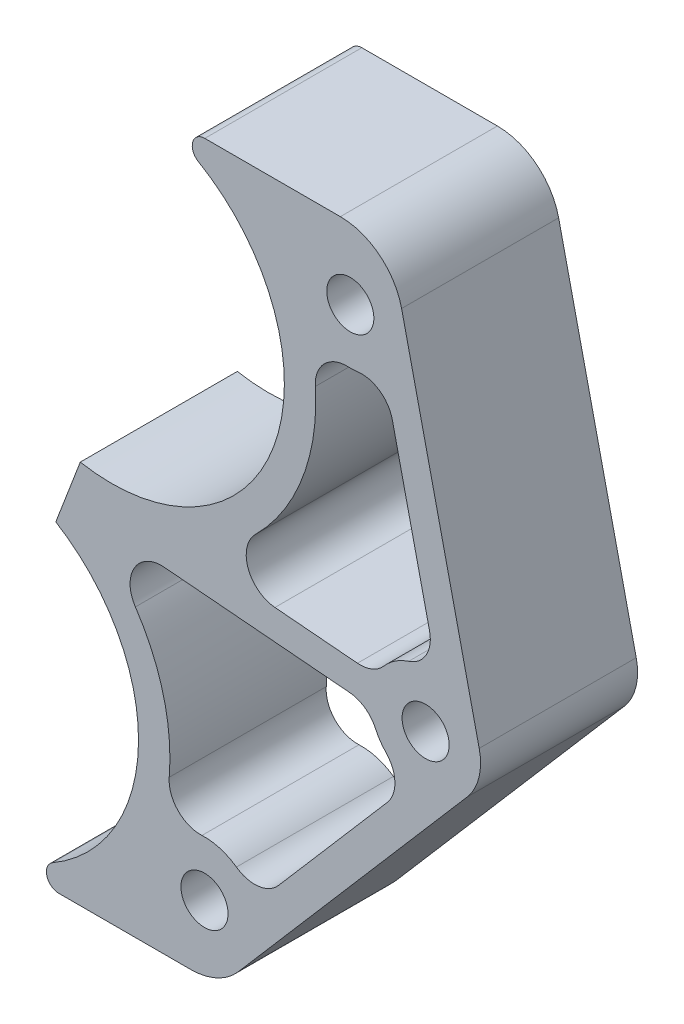
SolidWorks part; units mm, degrees
material "6061-T6 (SS)"
ref_plane "Front Plane" through (0, 0, 0) normal (0, 0, 1) x (1, 0, 0)
ref_plane "Top Plane" through (0, 0, 0) normal (0, 1, 0) x (1, 0, 0)
ref_plane "Right Plane" through (0, 0, 0) normal (1, 0, 0) x (0, 0, -1)
sketch "Sketch1" plane through (0, 0, 0) normal (0, 0, 1) x (1, 0, 0)
  line L0 (-29.4864, -77.1042) -> (0, 0) construction
  line L1 (-17.0114, -44.4832) -> (-12.475, -32.621)
  line L2 (-29.4864, -112.0292) -> (-29.4864, -117.5664)
  line L3 (-29.4864, -117.5664) -> (41.2306, -117.5664)
  line L4 (73.869, -111.2164) -> (73.869, -30.1792) construction
  line L5 (17.0334, -117.5664) -> (71.9024, -53.8526)
  line L6 (55.3346, 39.5732) -> (0, 39.5732)
  line L7 (0, 39.5732) -> (0, 34.925)
  line L8 (74.3193, -44.1435) -> (55.3346, 39.5732)
  line L9 (74.3193, -44.1435) -> (58.9814, 23.4919) construction
  line L10 (-6.2488, -111.2164) -> (41.2306, -111.2164) construction
  line L11 (10.6196, -44.2711) -> (48.1064, -47.4625)
  line L12 (33.0193, -40.1207) -> (49.7043, -41.5411)
  line L13 (27.1941, -105.7679) -> (71.9024, -53.8526) construction
  line L14 (33.7304, -88.4469) -> (55.7427, -62.8862)
  line L16 (64.2806, -28.5883) -> (56.7506, 4.6169)
  line L17 (-8.9876, -41.2793) -> (-8.6366, -40.3613) construction
  line L18 (41.2306, -111.2164) -> (73.869, -111.2164) construction
  line L19 (73.869, -30.1792) -> (73.869, 33.2232) construction
  line L20 (73.869, 33.2232) -> (24.4917, 33.2232) construction
  line L21 (24.4917, 33.2232) -> (24.4917, 33.2232) construction
  line L22 (-6.2488, -111.2164) -> (-6.2488, -111.2164) construction
  line L23 (80.219, 39.5732) -> (0, 39.5732) construction
  line L24 (68.1266, -45.5478) -> (52.7887, 22.0876) construction
  line L25 (22.3824, -101.6242) -> (67.0908, -49.7089) construction
  line L27 (0, 0) -> (24.1157, 0) construction
  line L29 (41.2306, -117.5664) -> (80.219, -117.5664) construction
  line L30 (80.219, -117.5664) -> (80.219, -30.1792) construction
  line L32 (80.219, -30.1792) -> (80.219, 39.5732) construction
  arc A0 (-12.475, -32.621) -> (0, 34.925) centre (0, 0) ccw
  arc A1 (-29.4864, -112.0292) -> (-17.0114, -44.4832) centre (-29.4864, -77.1042) ccw
  arc A2 (11.6451, -80.5432) -> (4.8053, -54.1324) centre (-29.4864, -77.1042) ccw
  arc A3 (29.0835, -29.2878) -> (41.1888, 2.666) centre (0, 0) ccw
  arc A4 (47.7926, 9.4205) -> (49.7222, 9.5073) centre (48.26, 20.5232) ccw
  circle A5 centre (48.26, 20.5232) radius 4.7625
  arc A6 (-8.6366, -40.3613) -> (24.4917, 33.2232) centre (0, 0) ccw construction
  arc A7 (25.2296, -89.4716) -> (18.2642, -87.4156) centre (18.7736, -98.5164) ccw
  arc A8 (-6.2488, -111.2164) -> (-8.9876, -41.2793) centre (-29.4864, -77.1042) ccw construction
  circle A9 centre (18.7736, -98.5164) radius 4.7625
  arc A10 (33.7304, -88.4469) -> (25.2296, -89.4716) centre (28.9187, -84.3032) cw
  arc A11 (53.3547, -51.1756) -> (48.1064, -47.4625) centre (47.5677, -53.7896) ccw
  arc A12 (53.3547, -51.1756) -> (55.4951, -54.3274) centre (63.482, -46.6011) ccw
  circle A13 centre (63.482, -46.6011) radius 4.7625
  arc A14 (29.0835, -29.2878) -> (33.0193, -40.1207) centre (33.5579, -33.7936) ccw
  arc A15 (4.8053, -54.1324) -> (10.6196, -44.2711) centre (10.081, -50.5982) cw
  arc A16 (49.7043, -41.5411) -> (55.0571, -39.3548) centre (50.2429, -35.214) ccw
  arc A17 (71.9024, -53.8526) -> (74.3193, -44.1435) centre (63.482, -46.6011) ccw
  arc A18 (60.0494, -36.0321) -> (55.0571, -39.3548) centre (63.482, -46.6011) ccw
  arc A19 (18.2642, -87.4156) -> (11.6451, -80.5432) centre (17.9731, -81.0723) cw
  arc A20 (55.7427, -62.8862) -> (55.4951, -54.3274) centre (50.9311, -58.7425) ccw
  arc A21 (64.2806, -28.5883) -> (60.0494, -36.0321) centre (58.0878, -29.9926) cw
  arc A22 (56.7506, 4.6169) -> (49.7222, 9.5073) centre (50.5578, 3.2125) ccw
  arc A23 (47.7926, 9.4205) -> (41.1888, 2.666) centre (47.5256, 3.0762) ccw
  point P69 (65.9061, -35.7562)
  dimension "D1" = 69.85
  dimension "D2" = 69.85
  dimension "D7" = 22.225
  dimension "D9" = 48.26
  dimension "D8" = 19.05
  dimension "D12" = 22.225
  dimension "D11" = 9.525
  dimension "D13" = 9.525
  dimension "D16" = 9.525
  dimension "D17" = 22.225
  dimension "D20" = 6.35
  dimension "D18" = 6.35
  dimension "D21" = 6.35
  dimension "D22" = 6.35
  dimension "D23" = 6.35
  dimension "D24" = 6.35
  dimension "D25" = 6.35
  dimension "D3" = 82.55
  dimension "D4" = 5.5372
  dimension "D5" = 4.6482
  dimension "D10" = 110.928
  dimension "D14" = 19.05
  dimension "D15" = 48.26
  dimension "D6" = 6.35
  dimension "D19" = 6.35
extrude "Boss-Extrude1" add sketch "Sketch1" along normal blind 31.75 contours L5 A17 L8 L6 L7 A0 L1 A1 L2 L3 A23 A4 A22 L16 A21 A18 A16 L12 A14 A3 A20 L14 A10 A7 A19 A2 A15 L11 A11 A12 A5 A9 A13
sketch "Sketch2" plane through (0, 0, 0) normal (-0.934, 0.3572, 0) x (0, 0, 1)
  line L0 (0, -41.275) -> (31.75, -41.275) construction
  circle A0 centre (7.9375, -41.275) radius 2.4892
  circle A1 centre (23.8125, -41.275) radius 2.4892
  dimension "D1" = 4.9784
  dimension "D2" = 4.9784
  dimension "D3" = 15.875
extrude "Cut-Extrude1" cut sketch "Sketch2" against normal blind 25.4
sketch "Sketch3" plane through (0, 0, 31.75) normal (0, 0, 1) x (1, 0, 0)
  line L0 (-17.0114, -44.4832) -> (-12.475, -32.621)
  line L1 (0, 34.925) -> (64.9871, 34.925)
  line L2 (0, 34.925) -> (0, 44.1699)
  line L3 (0, 44.1699) -> (64.9871, 44.1699)
  line L4 (64.9871, 34.925) -> (64.9871, 44.1699)
  line L5 (-29.4864, -112.0292) -> (31.471, -112.0292)
  line L6 (-29.4864, -112.0292) -> (-29.4864, -123.5063)
  line L7 (-29.4864, -123.5063) -> (31.471, -123.5063)
  line L8 (31.471, -112.0292) -> (31.471, -123.5063)
  line L9 (-12.475, -32.621) -> (-5.6765, -32.621)
  line L10 (-5.6765, -32.621) -> (-11.8621, -48.7958)
  line L11 (-11.8621, -48.7958) -> (-17.0114, -44.4832)
  dimension "D1" = 6.35
extrude "Cut-Extrude2" cut sketch "Sketch3" against normal through all
fillet "Fillet1" radius 2.54 2 edges at (-29.4864, -112.0292, 15.875) (0, 34.925, 15.875)
fillet "Fillet2" radius 12.7 2 edges at (21.802, -112.0292, 15.875) (56.3887, 34.925, 15.875)
